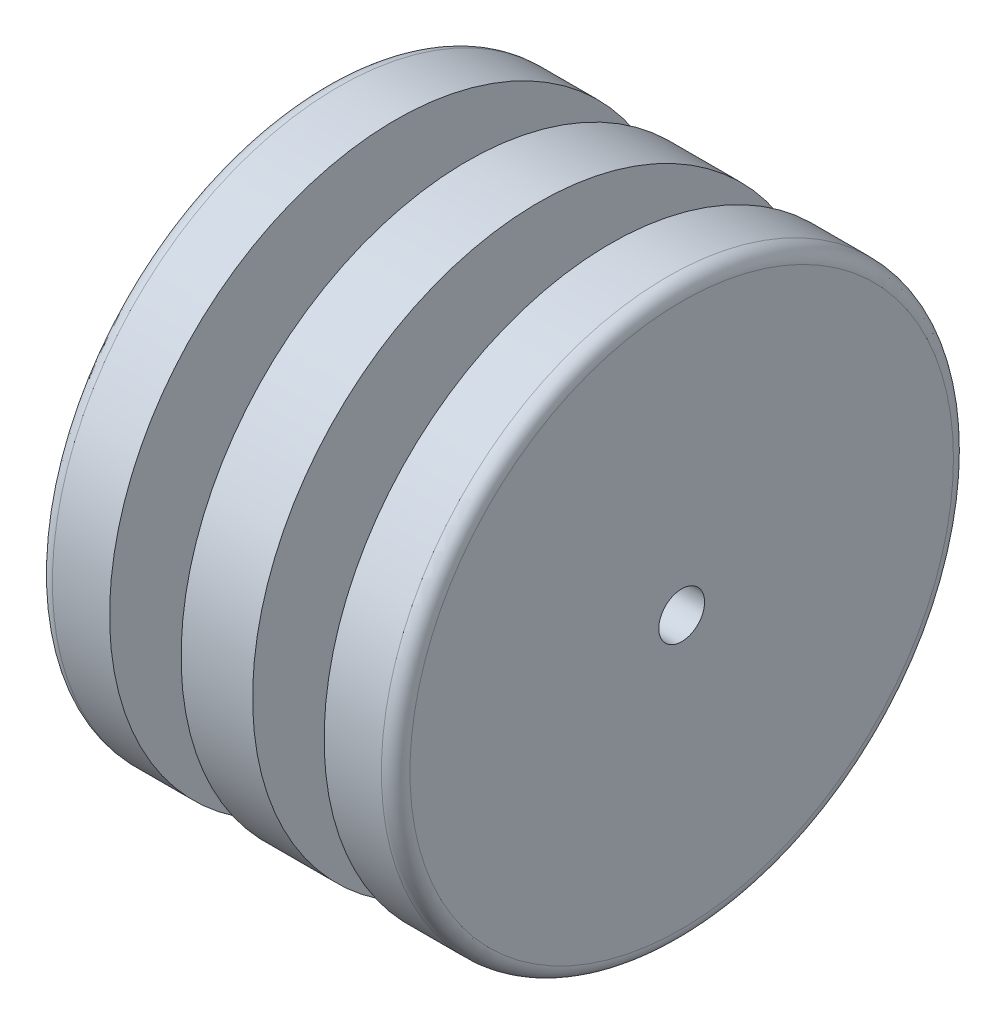
SolidWorks part; units mm, degrees
ref_plane "Front Plane" through (0, 0, 0) normal (0, 0, 1) x (1, 0, 0)
ref_plane "Top Plane" through (0, 0, 0) normal (0, 1, 0) x (1, 0, 0)
ref_plane "Right Plane" through (0, 0, 0) normal (1, 0, 0) x (0, 0, -1)
sketch "Sketch1" plane through (0, 0, 0) normal (1, 0, 0) x (0, 0, -1)
  circle A0 centre (0, 0) radius 20
  dimension "D1" = 40
extrude "Boss-Extrude1" add sketch "Sketch1" along normal blind 5
ref_plane "Plane1" through (5, 0, 0) normal (1, 0, 0) x (0, 0, -1)
sketch "Sketch2" plane through (5, 0, 0) normal (1, 0, 0) x (0, 0, -1)
  circle A0 centre (0, 0) radius 12.5
  dimension "D1" = 25
extrude "Boss-Extrude2" add sketch "Sketch2" along normal blind 5
ref_plane "Plane2" through (10, 0, 0) normal (1, 0, 0) x (0, 0, -1)
sketch "Sketch3" plane through (10, 0, 0) normal (1, 0, 0) x (0, 0, -1)
  circle A0 centre (0, 0) radius 20
  dimension "D1" = 40
extrude "Boss-Extrude3" add sketch "Sketch3" along normal blind 5
ref_plane "Plane3" through (15, 0, 0) normal (1, 0, 0) x (0, 0, -1)
sketch "Sketch4" plane through (15, 0, 0) normal (1, 0, 0) x (0, 0, -1)
  circle A0 centre (0, 0) radius 12.5
  dimension "D1" = 25
extrude "Boss-Extrude4" add sketch "Sketch4" along normal blind 5
ref_plane "Plane4" through (20, 0, 0) normal (1, 0, 0) x (0, 0, -1)
sketch "Sketch5" plane through (20, 0, 0) normal (1, 0, 0) x (0, 0, -1)
  circle A0 centre (0, 0) radius 20
  dimension "D1" = 40
extrude "Boss-Extrude5" add sketch "Sketch5" along normal blind 5
fillet "Fillet1" radius 1 2 edges at (0, 0, -20) (25, 0, -20)
ref_plane "Plane5" through (25, 0, 0) normal (1, 0, 0) x (0, 0, -1)
sketch "Sketch6" plane through (25, 0, 0) normal (1, 0, 0) x (0, 0, -1)
  circle A0 centre (0, 0) radius 1.6
  dimension "D1" = 3.2
extrude "Cut-Extrude1" cut sketch "Sketch6" against normal blind 25
